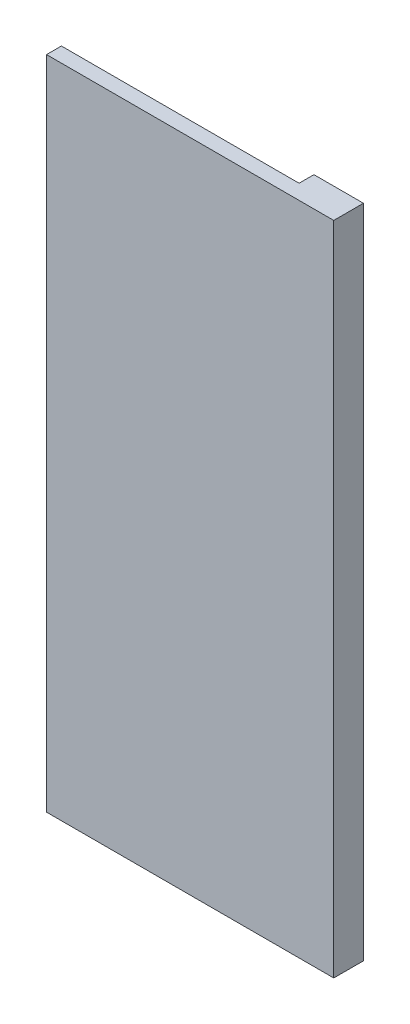
SolidWorks part; units mm, degrees
ref_plane "Front Plane" through (0, 0, 0) normal (0, 0, 1) x (1, 0, 0)
ref_plane "Top Plane" through (0, 0, 0) normal (0, 1, 0) x (1, 0, 0)
ref_plane "Right Plane" through (0, 0, 0) normal (1, 0, 0) x (0, 0, -1)
sketch "Sketch1" plane through (0, 0, 0) normal (0, 0, 1) x (1, 0, 0)
  line L1 (-48, 245) -> (68, 245)
  line L2 (-48, 245) -> (-48, -20)
  line L3 (-48, -20) -> (68, -20)
  line L4 (68, 245) -> (68, -20)
  line L5 (-48, 245) -> (48, 245)
  line L6 (-48, 245) -> (-48, 0)
  line L7 (-48, 0) -> (48, 0)
  line L8 (48, 245) -> (48, 0)
  dimension "D1" = 20
  dimension "D2" = 20
extrude "Boss-Extrude1" add sketch "Sketch1" against normal blind 6 contours L1 L8 L7 L2 L3 L4
sketch "Sketch2" plane through (0, 0, 0) normal (0, 0, 1) x (1, 0, 0)
  line L1 (68, -20) -> (-48, -20)
  line L2 (68, -20) -> (68, 245)
  line L3 (68, 245) -> (-48, 245)
  line L4 (-48, -20) -> (-48, 245)
extrude "Boss-Extrude2" add sketch "Sketch2" along normal blind 6
sketch "Sketch3" plane through (0, 0, -6) normal (0, 0, -1) x (-1, 0, 0)
  circle A0 centre (-48, 0) radius 10
  dimension "D1" = 20
extrude "Cut-Extrude1" cut sketch "Sketch3" against normal up to surface (6 mm away) up to face at (0, 122.5, 0)
